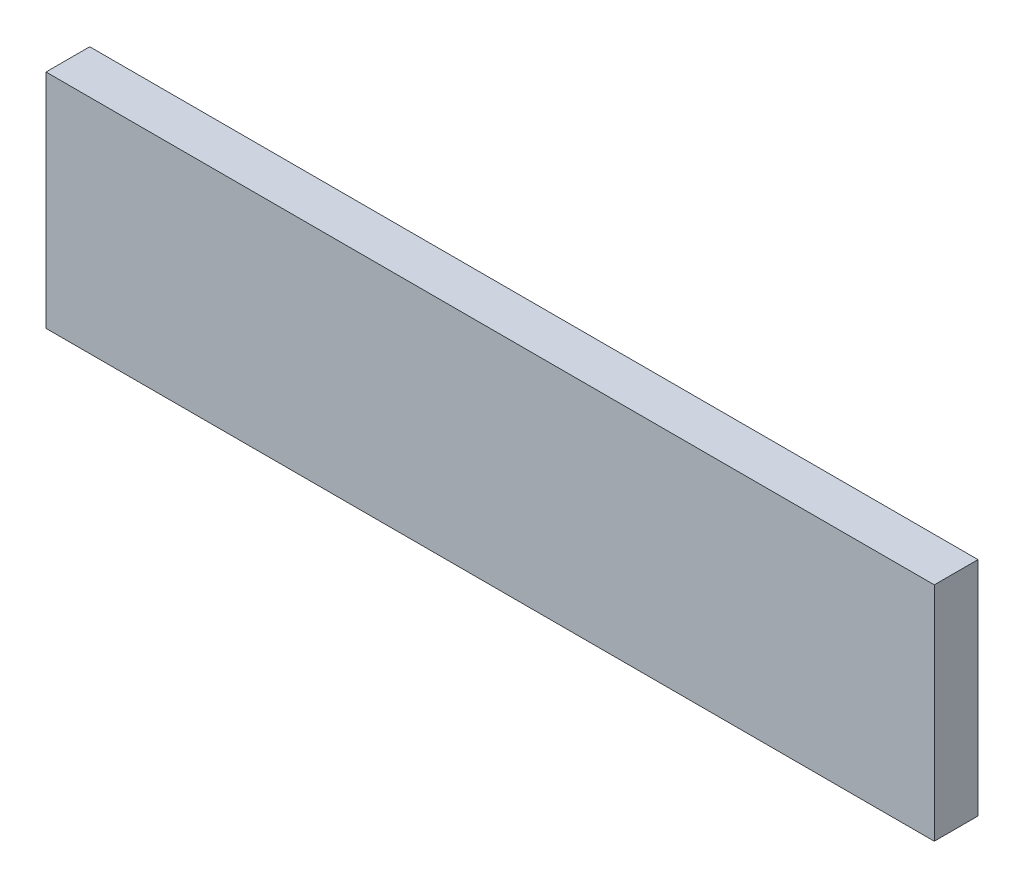
SolidWorks part; units mm, degrees
ref_plane "Front Plane" through (0, 0, 0) normal (0, 0, 1) x (1, 0, 0)
ref_plane "Top Plane" through (0, 0, 0) normal (0, 1, 0) x (1, 0, 0)
ref_plane "Right Plane" through (0, 0, 0) normal (1, 0, 0) x (0, 0, -1)
sketch "Sketch1" plane through (0, 0, 0) normal (0, 0, 1) x (1, 0, 0)
  line L1 (-72.4759, 34.8925) -> (29.1241, 34.8925)
  line L2 (-72.4759, 34.8925) -> (-72.4759, 9.4925)
  line L3 (-72.4759, 9.4925) -> (29.1241, 9.4925)
  line L4 (29.1241, 34.8925) -> (29.1241, 9.4925)
  dimension "D1" = 101.6
  dimension "D2" = 25.4
extrude "Boss-Extrude1" add sketch "Sketch1" along normal blind 5
